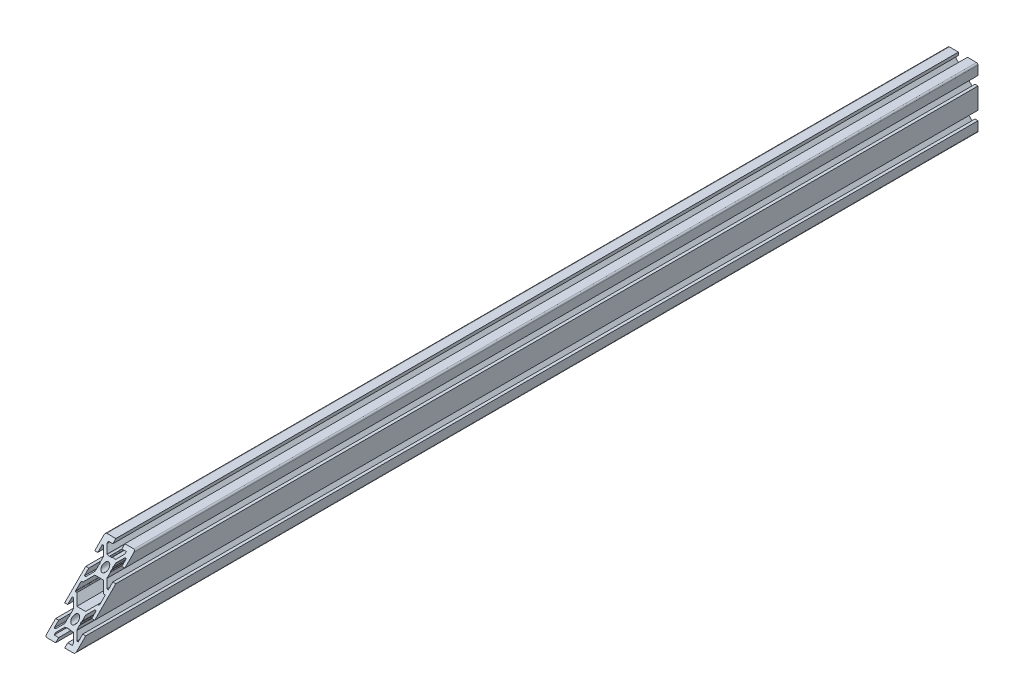
SolidWorks part; units mm, degrees
material "1060 Alloy"
ref_plane "Front Plane" through (0, 0, 0) normal (0, 0, 1) x (1, 0, 0)
ref_plane "Top Plane" through (0, 0, 0) normal (0, 1, 0) x (1, 0, 0)
ref_plane "Right Plane" through (0, 0, 0) normal (1, 0, 0) x (0, 0, -1)
ref_plane "Plane1" through (0, 0, -600) normal (0, 0, -1) x (-1, 0, 0)
sketch "Sketch1" plane through (0, 0, -600) normal (0, 0, -1) x (-1, 0, 0)
  line L0 (8, 1.7) -> (8, -1.7)
  line L1 (7.7, -2) -> (7.0636, -2)
  line L2 (6.8515, -2.0879) -> (2.9393, -6)
  line L3 (2.9393, -6) -> (-2.9393, -6)
  line L4 (-2.9393, -6) -> (-6.8515, -2.0879)
  line L5 (-7.0636, -2) -> (-7.7, -2)
  line L6 (-8, -1.7) -> (-8, 1.7)
  line L7 (-7.7, 2) -> (-7.0636, 2)
  line L8 (-6.8515, 2.0879) -> (-2.9393, 6)
  line L9 (-2.9393, 6) -> (2.9393, 6)
  line L10 (2.9393, 6) -> (6.8515, 2.0879)
  line L11 (7.0636, 2) -> (7.7, 2)
  line L12 (10, -7) -> (10, 7)
  line L13 (10, 7) -> (8, 7)
  line L14 (8, 7) -> (8, 4)
  line L15 (8, 4) -> (7.0607, 4)
  line L16 (7.0607, 4) -> (4, 7.0607)
  line L17 (4, 7.0607) -> (4, 7.5)
  line L18 (4, 7.5) -> (3.751, 8.7811)
  line L19 (3.751, 8.7811) -> (3.933, 9.0964)
  line L20 (3.933, 9.5964) -> (3.7, 10)
  line L21 (3.7, 10) -> (3.933, 10.4036)
  line L22 (4, 10.6536) -> (4, 12.9393)
  line L23 (4, 12.9393) -> (7.0607, 16)
  line L24 (7.0607, 16) -> (8, 16)
  line L25 (8, 16) -> (8, 13)
  line L26 (8, 13) -> (10, 13)
  line L27 (10, 13) -> (10, 19)
  line L28 (9, 20) -> (3, 20)
  line L29 (3, 20) -> (3, 18)
  line L30 (3, 18) -> (6, 18)
  line L31 (6, 18) -> (6, 17.0607)
  line L32 (6, 17.0607) -> (2.9393, 14)
  line L33 (2.9393, 14) -> (2.5, 14)
  line L34 (2.5, 14) -> (1.2189, 13.751)
  line L35 (1.2189, 13.751) -> (0.9036, 13.933)
  line L36 (0.4036, 13.933) -> (0, 13.7)
  line L37 (0, 13.7) -> (-0.4036, 13.933)
  line L38 (-0.6536, 14) -> (-2.9393, 14)
  line L39 (-2.9393, 14) -> (-6, 17.0607)
  line L40 (-6, 17.0607) -> (-6, 18)
  line L41 (-6, 18) -> (-3, 18)
  line L42 (-3, 18) -> (-3, 20)
  line L43 (-3, 20) -> (-9, 20)
  line L44 (-10, 19) -> (-10, 13)
  line L45 (-10, 13) -> (-8, 13)
  line L46 (-8, 13) -> (-8, 16)
  line L47 (-8, 16) -> (-7.0607, 16)
  line L48 (-7.0607, 16) -> (-4, 12.9393)
  line L49 (-4, 12.9393) -> (-4, 12.5)
  line L50 (-4, 12.5) -> (-3.751, 11.2189)
  line L51 (-3.751, 11.2189) -> (-3.933, 10.9036)
  line L52 (-3.933, 10.4036) -> (-3.7, 10)
  line L53 (-3.7, 10) -> (-3.933, 9.5964)
  line L54 (-4, 9.3464) -> (-4, 7.0607)
  line L55 (-4, 7.0607) -> (-7.0607, 4)
  line L56 (-7.0607, 4) -> (-8, 4)
  line L57 (-8, 4) -> (-8, 7)
  line L58 (-8, 7) -> (-10, 7)
  line L59 (-10, 7) -> (-10, -7)
  line L60 (-10, -7) -> (-8, -7)
  line L61 (-8, -7) -> (-8, -4)
  line L62 (-8, -4) -> (-7.0607, -4)
  line L63 (-7.0607, -4) -> (-4, -7.0607)
  line L64 (-4, -7.0607) -> (-4, -9.3464)
  line L65 (-3.933, -9.5964) -> (-3.7, -10)
  line L66 (-3.7, -10) -> (-3.933, -10.4036)
  line L67 (-3.933, -10.9036) -> (-3.751, -11.2189)
  line L68 (-3.751, -11.2189) -> (-4, -12.5)
  line L69 (-4, -12.5) -> (-4, -12.9393)
  line L70 (-4, -12.9393) -> (-7.0607, -16)
  line L71 (-7.0607, -16) -> (-8, -16)
  line L72 (-8, -16) -> (-8, -13)
  line L73 (-8, -13) -> (-10, -13)
  line L74 (-10, -13) -> (-10, -19)
  line L75 (-9, -20) -> (-3, -20)
  line L76 (-3, -20) -> (-3, -18)
  line L77 (-3, -18) -> (-6, -18)
  line L78 (-6, -18) -> (-6, -17.0607)
  line L79 (-6, -17.0607) -> (-2.9393, -14)
  line L80 (-2.9393, -14) -> (-0.6536, -14)
  line L81 (-0.4036, -13.933) -> (0, -13.7)
  line L82 (0, -13.7) -> (0.4036, -13.933)
  line L83 (0.9036, -13.933) -> (1.2189, -13.751)
  line L84 (1.2189, -13.751) -> (2.5, -14)
  line L85 (2.5, -14) -> (2.9393, -14)
  line L86 (2.9393, -14) -> (6, -17.0607)
  line L87 (6, -17.0607) -> (6, -18)
  line L88 (6, -18) -> (3, -18)
  line L89 (3, -18) -> (3, -20)
  line L90 (3, -20) -> (9, -20)
  line L91 (10, -19) -> (10, -13)
  line L92 (10, -13) -> (8, -13)
  line L93 (8, -13) -> (8, -16)
  line L94 (8, -16) -> (7.0607, -16)
  line L95 (7.0607, -16) -> (4, -12.9393)
  line L96 (4, -12.9393) -> (4, -10.6536)
  line L97 (3.933, -10.4036) -> (3.7, -10)
  line L98 (3.7, -10) -> (3.933, -9.5964)
  line L99 (3.933, -9.0964) -> (3.751, -8.7811)
  line L100 (3.751, -8.7811) -> (4, -7.5)
  line L101 (4, -7.5) -> (4, -7.0607)
  line L102 (4, -7.0607) -> (7.0607, -4)
  line L103 (7.0607, -4) -> (8, -4)
  line L104 (8, -4) -> (8, -7)
  line L105 (8, -7) -> (10, -7)
  circle A0 centre (0, -10) radius 2.1
  circle A1 centre (0, 10) radius 2.1
  arc A2 (7.7, 2) -> (8, 1.7) centre (7.7, 1.7) cw
  arc A3 (8, -1.7) -> (7.7, -2) centre (7.7, -1.7) cw
  arc A4 (7.0636, -2) -> (6.8515, -2.0879) centre (7.0636, -2.3) ccw
  arc A5 (-6.8515, -2.0879) -> (-7.0636, -2) centre (-7.0636, -2.3) ccw
  arc A6 (-7.7, -2) -> (-8, -1.7) centre (-7.7, -1.7) cw
  arc A7 (-8, 1.7) -> (-7.7, 2) centre (-7.7, 1.7) cw
  arc A8 (-7.0636, 2) -> (-6.8515, 2.0879) centre (-7.0636, 2.3) ccw
  arc A9 (6.8515, 2.0879) -> (7.0636, 2) centre (7.0636, 2.3) ccw
  arc A10 (3.933, 9.0964) -> (3.933, 9.5964) centre (3.5, 9.3464) ccw
  arc A11 (3.933, 10.4036) -> (4, 10.6536) centre (3.5, 10.6536) ccw
  arc A12 (10, 19) -> (9, 20) centre (9, 19) ccw
  arc A13 (0.9036, 13.933) -> (0.4036, 13.933) centre (0.6536, 13.5) ccw
  arc A14 (-0.4036, 13.933) -> (-0.6536, 14) centre (-0.6536, 13.5) ccw
  arc A15 (-9, 20) -> (-10, 19) centre (-9, 19) ccw
  arc A16 (-3.933, 10.9036) -> (-3.933, 10.4036) centre (-3.5, 10.6536) ccw
  arc A17 (-3.933, 9.5964) -> (-4, 9.3464) centre (-3.5, 9.3464) ccw
  arc A18 (-4, -9.3464) -> (-3.933, -9.5964) centre (-3.5, -9.3464) ccw
  arc A19 (-3.933, -10.4036) -> (-3.933, -10.9036) centre (-3.5, -10.6536) ccw
  arc A20 (-10, -19) -> (-9, -20) centre (-9, -19) ccw
  arc A21 (-0.6536, -14) -> (-0.4036, -13.933) centre (-0.6536, -13.5) ccw
  arc A22 (0.4036, -13.933) -> (0.9036, -13.933) centre (0.6536, -13.5) ccw
  arc A23 (9, -20) -> (10, -19) centre (9, -19) ccw
  arc A24 (4, -10.6536) -> (3.933, -10.4036) centre (3.5, -10.6536) ccw
  arc A25 (3.933, -9.5964) -> (3.933, -9.0964) centre (3.5, -9.3464) ccw
  dimension "D1" = 4.2
  dimension "D3" = 0.3
  dimension "D4" = 0.3
  dimension "D5" = 0.3
  dimension "D6" = 0.3
  dimension "D7" = 0.3
  dimension "D8" = 0.3
  dimension "D9" = 0.3
  dimension "D10" = 0.5
  dimension "D11" = 0.5
  dimension "D12" = 1
  dimension "D13" = 0.5
  dimension "D14" = 0.5
  dimension "D15" = 1
  dimension "D16" = 0.5
  dimension "D17" = 0.5
  dimension "D18" = 0.5
  dimension "D19" = 0.5
  dimension "D20" = 0.4036
  dimension "D21" = 0.5
  dimension "D22" = 0.5
  dimension "D23" = 1
  dimension "D24" = 0.5
  dimension "D25" = 0.5
  dimension "D26" = 0.4036
  dimension "D27" = 0.6536
  dimension "D28" = 0.6536
  dimension "D29" = 0.9036
  dimension "D30" = 0.9036
  dimension "D31" = 1.2189
  dimension "D32" = 1.2189
  dimension "D33" = 2.5
  dimension "D34" = 2.5
  dimension "D35" = 2.9393
  dimension "D36" = 2.9393
  dimension "D37" = 3
  dimension "D38" = 3.5
  dimension "D39" = 6
  dimension "D40" = 6.8515
  dimension "D41" = 3.7
  dimension "D42" = 3.7
  dimension "D43" = 3.751
  dimension "D44" = 3.751
  dimension "D45" = 3.933
  dimension "D46" = 3.933
  dimension "D47" = 6.8515
  dimension "D48" = 7.0607
  dimension "D49" = 7.0607
  dimension "D50" = 7.0636
  dimension "D51" = 7.0636
  dimension "D52" = 8
  dimension "D53" = 10
  dimension "D54" = 3
  dimension "D55" = 4
  dimension "D56" = 6
  dimension "D57" = 6.8515
  dimension "D58" = 6.8515
  dimension "D59" = 7.0607
  dimension "D60" = 7.0607
  dimension "D61" = 0.4036
  dimension "D62" = 0.4036
  dimension "D63" = 0.6536
  dimension "D64" = 0.6536
  dimension "D65" = 2.9393
  dimension "D66" = 2.9393
  dimension "D67" = 8
  dimension "D68" = 2
  dimension "D69" = 3.5
  dimension "D70" = 3.5
  dimension "D71" = 3.7
  dimension "D72" = 3.7
  dimension "D73" = 3.751
  dimension "D74" = 3.751
  dimension "D75" = 3.933
  dimension "D76" = 3.933
  dimension "D77" = 4
  dimension "D78" = 6
  dimension "D79" = 7
  dimension "D80" = 7.0607
  dimension "D81" = 7.0607
  dimension "D82" = 7.5
  dimension "D83" = 8.7811
  dimension "D84" = 9.0964
  dimension "D85" = 9.3464
  dimension "D86" = 9.3464
  dimension "D87" = 9.5964
  dimension "D88" = 9.5964
  dimension "D89" = 10.4036
  dimension "D90" = 12.5
  dimension "D91" = 13
  dimension "D92" = 13.5
  dimension "D93" = 13.5
  dimension "D94" = 18
  dimension "D95" = 20
  dimension "D96" = 2
  dimension "D97" = 4
  dimension "D98" = 6
  dimension "D99" = 7
  dimension "D100" = 7.0607
  dimension "D101" = 7.0607
  dimension "D102" = 7.5
  dimension "D103" = 8.7811
  dimension "D104" = 9.0964
  dimension "D105" = 9.3464
  dimension "D106" = 9.3464
  dimension "D107" = 9.5964
  dimension "D108" = 9.5964
  dimension "D109" = 10.4036
  dimension "D110" = 12.5
  dimension "D111" = 13
  dimension "D112" = 18
extrude "Boss-Extrude1" add sketch "Sketch1" against normal blind 600
ref_plane "Plane2" through (0, 0, -300) normal (0, 0, 1) x (1, 0, 0)
sketch "Sketch3" plane through (10, 0, 0) normal (1, 0, 0) x (0, 0, -1)
  line L0 (0, -20) -> (40, 20)
  line L1 (0, 20) -> (600, 20) construction
  line L2 (40, 20) -> (0, 20)
  line L3 (0, 20) -> (0, -20)
  dimension "D1" = 45
extrude "Cut-Extrude2" cut sketch "Sketch3" against normal through all
sketch "Sketch4" plane through (10, 0, 0) normal (1, 0, 0) x (0, 0, -1)
  line L0 (590, 20) -> (590, -20) construction
  line L1 (40, 20) -> (600, 20) construction
  line L2 (0, -20) -> (600, -20) construction
  line L3 (600, 7) -> (600, -7) construction
  circle A0 centre (590, 10) radius 2
  circle A1 centre (590, -10) radius 2
  dimension "D2" = 10
  dimension "D4" = 4
  dimension "D5" = 4
  dimension "D1" = 10
  dimension "D3" = 10
extrude "Cut-Extrude3" cut sketch "Sketch4" against normal through all
